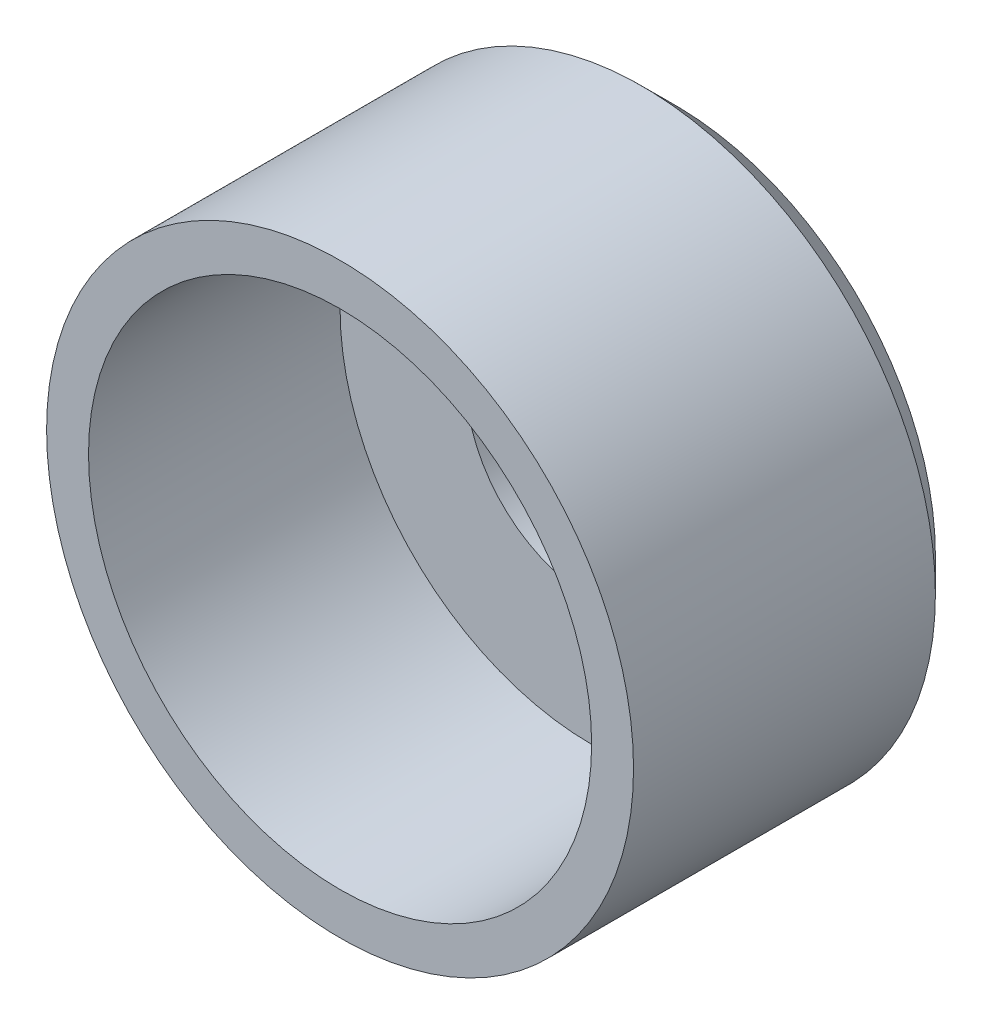
SolidWorks part; units mm, degrees
ref_plane "Front Plane" through (0, 0, 0) normal (0, 0, 1) x (1, 0, 0)
ref_plane "Top Plane" through (0, 0, 0) normal (0, 1, 0) x (1, 0, 0)
ref_plane "Right Plane" through (0, 0, 0) normal (1, 0, 0) x (0, 0, -1)
sketch "Sketch1" plane through (0, 0, 0) normal (0, 0, 1) x (1, 0, 0)
  circle A0 centre (0, 0) radius 17.5
  dimension "D1" = 35
extrude "Boss-Extrude1" add sketch "Sketch1" along normal blind 5
sketch "Sketch2" plane through (0, 0, 5) normal (0, 0, 1) x (1, 0, 0)
  circle A0 centre (0, 0) radius 17.5
  circle A1 centre (0, 0) radius 15
  dimension "D1" = 35
  dimension "D2" = 30
extrude "Boss-Extrude2" add sketch "Sketch2" along normal blind 15
sketch "Sketch3" plane through (0, 0, 0) normal (0, 0, -1) x (-1, 0, 0)
  circle A0 centre (0, 0) radius 7.5
  dimension "D1" = 15
extrude "Cut-Extrude1" cut sketch "Sketch3" against normal through all
chamfer "Chamfer1" distance 2 angle 45 1 edges at (17.5, 0, 0)
